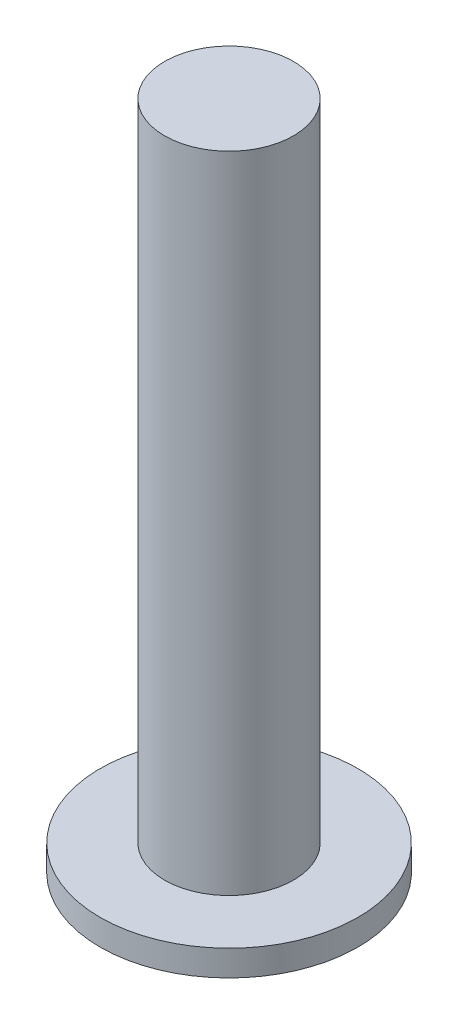
SolidWorks part; units mm, degrees
ref_plane "Front Plane" through (0, 0, 0) normal (0, 0, 1) x (1, 0, 0)
ref_plane "Top Plane" through (0, 0, 0) normal (0, 1, 0) x (1, 0, 0)
ref_plane "Right Plane" through (0, 0, 0) normal (1, 0, 0) x (0, 0, -1)
sketch "Sketch1" plane through (0, 0, 0) normal (0, 1, 0) x (1, 0, 0)
  circle A0 centre (0, 0) radius 50
extrude "Boss-Extrude1" add sketch "Sketch1" along normal blind 10
sketch "Sketch2" plane through (0, 10, 0) normal (0, 1, 0) x (1, 0, 0)
  circle A0 centre (0, 0) radius 25
extrude "Boss-Extrude2" add sketch "Sketch2" along normal blind 250 contours A0
